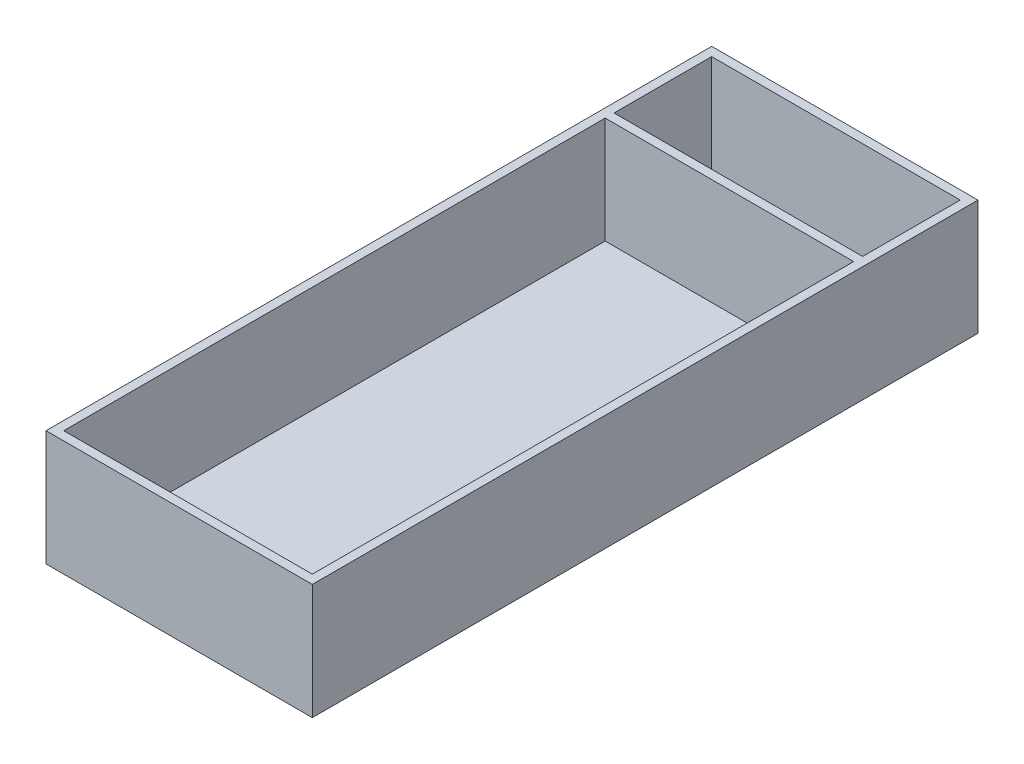
SolidWorks part; units mm, degrees
ref_plane "Front Plane" through (0, 0, 0) normal (0, 0, 1) x (1, 0, 0)
ref_plane "Top Plane" through (0, 0, 0) normal (0, 1, 0) x (1, 0, 0)
ref_plane "Right Plane" through (0, 0, 0) normal (1, 0, 0) x (0, 0, -1)
sketch "Sketch1" plane through (0, 0, 0) normal (0, 1, 0) x (1, 0, 0)
  line L1 (-35.56, -92.71) -> (35.56, -92.71)
  line L2 (-35.56, -92.71) -> (-35.56, 92.71)
  line L3 (-35.56, 92.71) -> (35.56, 92.71)
  line L4 (35.56, -92.71) -> (35.56, 92.71)
  line L5 (-35.56, -92.71) -> (35.56, 92.71) construction
  line L6 (-35.56, 92.71) -> (35.56, -92.71) construction
  point P0 (0, 0)
  dimension "D1" = 71.12
  dimension "D2" = 185.42
extrude "Extrude-Thin1" add sketch "Sketch1" along normal blind 30.48 thin
sketch "Sketch2" plane through (0, 0, 0) normal (0, -1, 0) x (1, 0, 0)
  line L5 (38.1, 95.25) -> (-38.1, 95.25)
  line L6 (38.1, 95.25) -> (38.1, -95.25)
  line L7 (38.1, -95.25) -> (-38.1, -95.25)
  line L8 (-38.1, 95.25) -> (-38.1, -95.25)
extrude "Boss-Extrude1" add sketch "Sketch2" along normal blind 2.54
sketch "Sketch4" plane through (0, 0, 0) normal (0, 1, 0) x (1, 0, 0)
  line L0 (-35.56, 92.71) -> (-35.56, -92.71) construction
  line L1 (-35.56, 64.77) -> (35.56, 64.77)
  line L2 (-35.56, 64.77) -> (-35.56, 62.23)
  line L3 (-35.56, 62.23) -> (35.56, 62.23)
  line L4 (35.56, 64.77) -> (35.56, 62.23)
  line L5 (35.56, -92.71) -> (35.56, 92.71) construction
  line L6 (-35.56, -92.71) -> (35.56, -92.71) construction
  point P10 (0, -92.71)
  dimension "D1" = 2.54
  dimension "D2" = 154.94
extrude "Boss-Extrude2" add sketch "Sketch4" along normal blind 30.48
